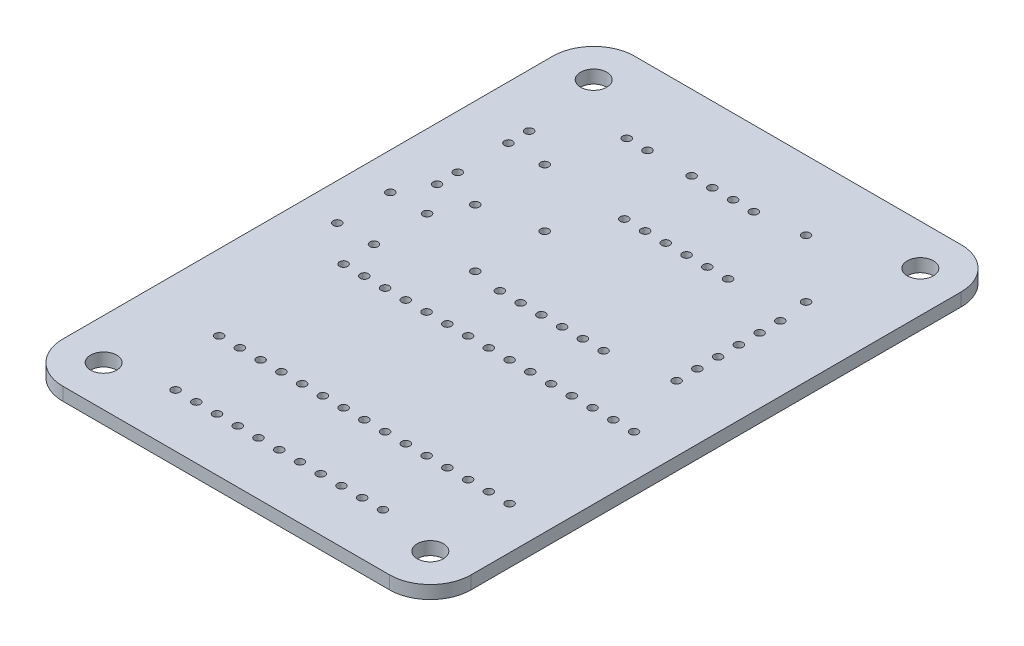
SolidWorks part; units mm, degrees
ref_plane "Front Plane" through (0, 0, 0) normal (0, 0, 1) x (1, 0, 0)
ref_plane "Top Plane" through (0, 0, 0) normal (0, 1, 0) x (1, 0, 0)
ref_plane "Right Plane" through (0, 0, 0) normal (1, 0, 0) x (0, 0, -1)
sketch "Sketch1" plane through (0, 0, 0) normal (0, 1, 0) x (1, 0, 0)
  line L1 (-25, -35) -> (25, -35)
  line L2 (-25, -35) -> (-25, 35)
  line L3 (-25, 35) -> (25, 35)
  line L4 (25, -35) -> (25, 35)
  line L5 (-25, -35) -> (25, 35) construction
  line L6 (-25, 35) -> (25, -35) construction
  point P0 (0, 0)
  dimension "D1" = 50
  dimension "D2" = 70
extrude "Boss-Extrude1" add sketch "Sketch1" along normal blind 1.6
fillet "Fillet2" radius 5 4 edges at (25, 0.8, 35) (25, 0.8, -35) (-25, 0.8, -35) (-25, 0.8, 35)
sketch "Sketch2" plane through (0, 1.6, 0) normal (0, 1, 0) x (1, 0, 0)
  line L1 (-20, -30) -> (20, -30) construction
  line L2 (-20, -30) -> (-20, 30) construction
  line L3 (-20, 30) -> (20, 30) construction
  line L4 (20, -30) -> (20, 30) construction
  line L5 (-20, -30) -> (20, 30) construction
  line L6 (-20, 30) -> (20, -30) construction
  line L8 (-25, 30) -> (-25, -30) construction
  line L9 (-20, -35) -> (20, -35) construction
  circle A0 centre (-20, 30) radius 1.6
  circle A1 centre (20, 30) radius 1.6
  circle A2 centre (20, -30) radius 1.6
  circle A3 centre (-20, -30) radius 1.6
  point P0 (0, 0)
  dimension "D1" = 3.2
  dimension "D2" = 5
  dimension "D3" = 5
extrude "Cut-Extrude1" cut sketch "Sketch2" against normal up to surface (1.6 mm away) up to face at (0, 0, 0)
sketch "Sketch3" plane through (0, 1.6, 0) normal (0, 1, 0) x (1, 0, 0)
  line L0 (-3.81, 25.8) -> (-1.27, 25.8) construction
  line L1 (-1.27, 25.8) -> (1.27, 25.8) construction
  line L2 (1.27, 25.8) -> (3.81, 25.8) construction
  line L3 (-11.75, 25.8) -> (-9.21, 25.8) construction
  line L4 (-15.76, -20.1) -> (-13.22, -20.1) construction
  line L5 (-13.22, -20.1) -> (-10.68, -20.1) construction
  line L6 (-10.68, -20.1) -> (-8.14, -20.1) construction
  line L7 (-8.14, -20.1) -> (-5.6, -20.1) construction
  line L8 (-5.6, -20.1) -> (-3.06, -20.1) construction
  line L9 (-3.06, -20.1) -> (-0.52, -20.1) construction
  line L10 (-0.52, -20.1) -> (2.02, -20.1) construction
  line L11 (2.02, -20.1) -> (4.56, -20.1) construction
  line L12 (4.56, -20.1) -> (7.1, -20.1) construction
  line L13 (7.1, -20.1) -> (9.64, -20.1) construction
  line L14 (9.64, -20.1) -> (12.18, -20.1) construction
  line L15 (12.18, -20.1) -> (14.72, -20.1) construction
  line L16 (14.72, -20.1) -> (17.26, -20.1) construction
  line L17 (17.26, -20.1) -> (19.8, -20.1) construction
  line L18 (-15.76, -4.86) -> (-13.22, -4.86) construction
  line L19 (-13.22, -4.86) -> (-10.68, -4.86) construction
  line L20 (-10.68, -4.86) -> (-8.14, -4.86) construction
  line L21 (-8.14, -4.86) -> (-5.6, -4.86) construction
  line L22 (-5.6, -4.86) -> (-3.06, -4.86) construction
  line L23 (-3.06, -4.86) -> (-0.52, -4.86) construction
  line L24 (-0.52, -4.86) -> (2.02, -4.86) construction
  line L25 (2.02, -4.86) -> (4.56, -4.86) construction
  line L26 (4.56, -4.86) -> (7.1, -4.86) construction
  line L27 (7.1, -4.86) -> (9.64, -4.86) construction
  line L28 (9.64, -4.86) -> (12.18, -4.86) construction
  line L29 (12.18, -4.86) -> (14.72, -4.86) construction
  line L30 (14.72, -4.86) -> (17.26, -4.86) construction
  line L31 (17.26, -4.86) -> (19.8, -4.86) construction
  line L32 (-3.35, 17.1) -> (-0.81, 17.1) construction
  line L33 (-0.81, 17.1) -> (1.73, 17.1) construction
  line L34 (1.73, 17.1) -> (4.27, 17.1) construction
  line L35 (4.27, 17.1) -> (6.81, 17.1) construction
  line L36 (6.81, 17.1) -> (9.35, 17.1) construction
  line L37 (-3.35, 1.86) -> (-0.81, 1.86) construction
  line L38 (-0.81, 1.86) -> (1.73, 1.86) construction
  line L39 (1.73, 1.86) -> (4.27, 1.86) construction
  line L40 (4.27, 1.86) -> (6.81, 1.86) construction
  line L41 (6.81, 1.86) -> (9.35, 1.86) construction
  line L42 (20, 35) -> (-20, 35) construction
  line L43 (25, -30) -> (25, 30) construction
  line L44 (-20, -35) -> (20, -35) construction
  line L45 (-12.7, -28.5) -> (-10.16, -28.5) construction
  line L46 (-10.16, -28.5) -> (-7.62, -28.5) construction
  line L47 (-7.62, -28.5) -> (-5.08, -28.5) construction
  line L48 (-5.08, -28.5) -> (-2.54, -28.5) construction
  line L49 (-2.54, -28.5) -> (0, -28.5) construction
  line L50 (0, -28.5) -> (2.54, -28.5) construction
  line L51 (2.54, -28.5) -> (5.08, -28.5) construction
  line L52 (5.08, -28.5) -> (7.62, -28.5) construction
  line L53 (7.62, -28.5) -> (10.16, -28.5) construction
  line L54 (10.16, -28.5) -> (12.7, -28.5) construction
  line L55 (-18.5, 20.6) -> (-18.5, 18.06) construction
  line L56 (17, 3.15) -> (17, 5.69) construction
  line L57 (17, 5.69) -> (17, 8.23) construction
  line L58 (17, 8.23) -> (17, 10.77) construction
  line L59 (17, 10.77) -> (17, 13.31) construction
  line L60 (17, 13.31) -> (17, 15.85) construction
  line L61 (-18.5, 18.06) -> (-18.5, 11.86) construction
  line L62 (-18.5, 11.86) -> (-18.5, 9.32) construction
  line L63 (-25, 30) -> (-25, -30) construction
  line L64 (-16, 5.6) -> (-16, -0.9) construction
  line L65 (-16, -0.9) -> (-20.5, -0.9) construction
  line L66 (-20.5, -0.9) -> (-20.5, 5.6) construction
  line L67 (-20.5, 5.6) -> (-16, 5.6) construction
  line L68 (-14, 9.5) -> (-6.9289, 2.4289) construction
  line L69 (9.5, 26.5) -> (16.5711, 19.4289) construction
  line L70 (-14, 18) -> (-6.9289, 10.9289) construction
  circle A4 centre (-3.81, 25.8) radius 0.5
  circle A5 centre (-1.27, 25.8) radius 0.5
  circle A6 centre (1.27, 25.8) radius 0.5
  circle A7 centre (3.81, 25.8) radius 0.5
  circle A8 centre (-11.75, 25.8) radius 0.5
  circle A9 centre (-9.21, 25.8) radius 0.5
  circle A33 centre (-15.76, -20.1) radius 0.5
  circle A34 centre (-13.22, -20.1) radius 0.5
  circle A35 centre (-10.68, -20.1) radius 0.5
  circle A36 centre (-8.14, -20.1) radius 0.5
  circle A37 centre (-5.6, -20.1) radius 0.5
  circle A38 centre (-3.06, -20.1) radius 0.5
  circle A39 centre (-0.52, -20.1) radius 0.5
  circle A40 centre (2.02, -20.1) radius 0.5
  circle A41 centre (4.56, -20.1) radius 0.5
  circle A42 centre (7.1, -20.1) radius 0.5
  circle A43 centre (9.64, -20.1) radius 0.5
  circle A44 centre (12.18, -20.1) radius 0.5
  circle A45 centre (14.72, -20.1) radius 0.5
  circle A46 centre (17.26, -20.1) radius 0.5
  circle A47 centre (19.8, -20.1) radius 0.5
  circle A48 centre (-15.76, -4.86) radius 0.5
  circle A49 centre (-13.22, -4.86) radius 0.5
  circle A50 centre (-10.68, -4.86) radius 0.5
  circle A51 centre (-8.14, -4.86) radius 0.5
  circle A52 centre (-5.6, -4.86) radius 0.5
  circle A53 centre (-3.06, -4.86) radius 0.5
  circle A54 centre (-0.52, -4.86) radius 0.5
  circle A55 centre (2.02, -4.86) radius 0.5
  circle A56 centre (4.56, -4.86) radius 0.5
  circle A57 centre (7.1, -4.86) radius 0.5
  circle A58 centre (9.64, -4.86) radius 0.5
  circle A59 centre (12.18, -4.86) radius 0.5
  circle A60 centre (14.72, -4.86) radius 0.5
  circle A61 centre (17.26, -4.86) radius 0.5
  circle A62 centre (19.8, -4.86) radius 0.5
  circle A63 centre (-3.35, 1.86) radius 0.5
  circle A64 centre (-0.81, 1.86) radius 0.5
  circle A65 centre (1.73, 1.86) radius 0.5
  circle A66 centre (4.27, 1.86) radius 0.5
  circle A67 centre (6.81, 1.86) radius 0.5
  circle A68 centre (9.35, 1.86) radius 0.5
  circle A69 centre (-3.35, 17.1) radius 0.5
  circle A70 centre (-0.81, 17.1) radius 0.5
  circle A71 centre (1.73, 17.1) radius 0.5
  circle A72 centre (4.27, 17.1) radius 0.5
  circle A73 centre (6.81, 17.1) radius 0.5
  circle A74 centre (9.35, 17.1) radius 0.5
  circle A75 centre (-12.7, -28.5) radius 0.5
  circle A76 centre (-10.16, -28.5) radius 0.5
  circle A77 centre (-7.62, -28.5) radius 0.5
  circle A78 centre (-5.08, -28.5) radius 0.5
  circle A79 centre (-2.54, -28.5) radius 0.5
  circle A80 centre (0, -28.5) radius 0.5
  circle A81 centre (2.54, -28.5) radius 0.5
  circle A82 centre (5.08, -28.5) radius 0.5
  circle A83 centre (7.62, -28.5) radius 0.5
  circle A84 centre (10.16, -28.5) radius 0.5
  circle A85 centre (12.7, -28.5) radius 0.5
  circle A92 centre (17, 15.85) radius 0.5
  circle A93 centre (17, 13.31) radius 0.5
  circle A94 centre (17, 10.77) radius 0.5
  circle A95 centre (17, 3.15) radius 0.5
  circle A96 centre (17, 5.69) radius 0.5
  circle A97 centre (17, 8.23) radius 0.5
  circle A98 centre (-18.5, 20.6) radius 0.5
  circle A99 centre (-18.5, 18.06) radius 0.5
  circle A100 centre (-18.5, 11.86) radius 0.5
  circle A101 centre (-18.5, 9.32) radius 0.5
  circle A102 centre (-16, 5.6) radius 0.5
  circle A103 centre (-16, -0.9) radius 0.5
  circle A104 centre (-20.5, -0.9) radius 0.5
  circle A105 centre (-20.5, 5.6) radius 0.5
  circle A106 centre (9.5, 26.5) radius 0.5
  circle A107 centre (16.5711, 19.4289) radius 0.5
  circle A108 centre (-6.9289, 10.9289) radius 0.5
  circle A109 centre (-14, 18) radius 0.5
  circle A110 centre (-14, 9.5) radius 0.5
  circle A111 centre (-6.9289, 2.4289) radius 0.5
  point P72 (18.53, -4.86)
  point P73 (18.53, -20.1)
  point P101 (0, 35)
  point P102 (0, 25.8)
  point P130 (0, -35)
  point P171 (0, 0)
  point P172 (-6.8571, 9.0834)
  point P173 (0, 0)
  dimension "D1" = 1
  dimension "D3" = 1
  dimension "D5" = 2.54
  dimension "D6" = 1
  dimension "D8" = 1
  dimension "D9" = 1
  dimension "D20" = 1
  dimension "D23" = 1
  dimension "D26" = 1
  dimension "D29" = 6.5
  dimension "D33" = 1
  dimension "D37" = 1
  dimension "D2" = 2.54
  dimension "D4" = 2.54
  dimension "D7" = 2.54
  dimension "D10" = 2.54
  dimension "D11" = 15.24
  dimension "D12" = 15.24
  dimension "D13" = 5.4
  dimension "D14" = 9.2
  dimension "D15" = 15.65
  dimension "D16" = 17.9
  dimension "D17" = 5.2
  dimension "D18" = 14.9
  dimension "D19" = 2.54
  dimension "D21" = 6.5
  dimension "D22" = 2.54
  dimension "D24" = 8
  dimension "D25" = 19.15
  dimension "D27" = 2.54
  dimension "D28" = 6.2
  dimension "D30" = 14.4
  dimension "D31" = 6.5
  dimension "D32" = 4.5
  dimension "D34" = 4.5
  dimension "D35" = 29.4
  dimension "D36" = 10
  dimension "D38" = 8.5
  dimension "D39" = 11
  dimension "D40" = 17
  dimension "D41" = 45
  dimension "D42" = 15.5
  dimension "D43" = 8.5
extrude "Cut-Extrude2" cut sketch "Sketch3" against normal up to surface (1.6 mm away) up to face at (-20, 0, 28.4)
